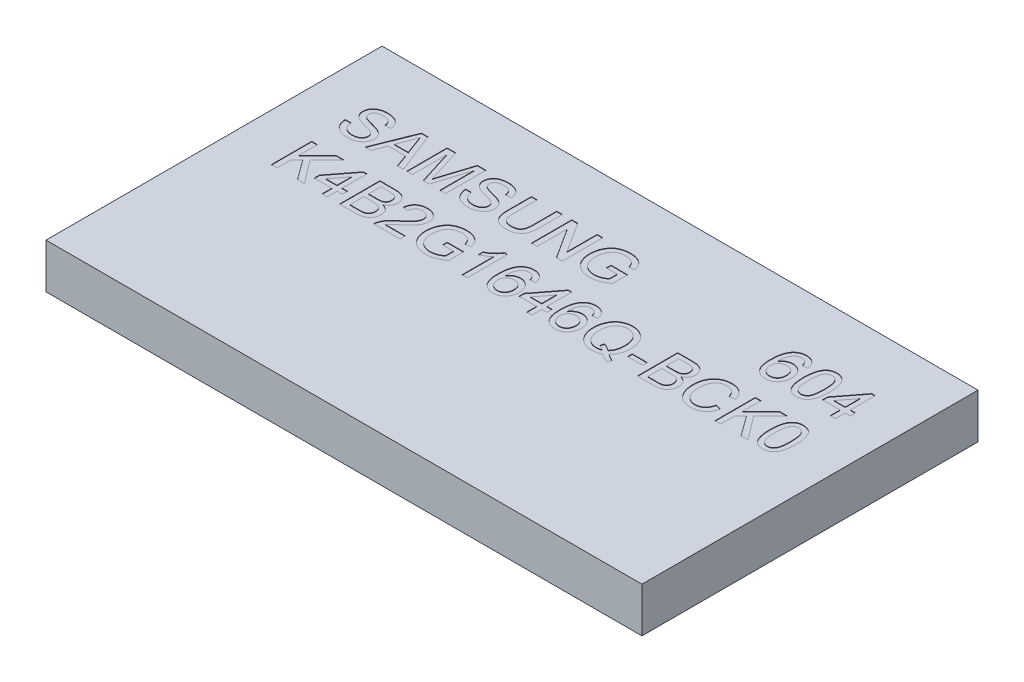
SolidWorks part; units mm, degrees
ref_plane "Спереди" through (0, 0, 0) normal (0, 0, 1) x (1, 0, 0)
ref_plane "Сверху" through (0, 0, 0) normal (0, 1, 0) x (1, 0, 0)
ref_plane "Справа" through (0, 0, 0) normal (1, 0, 0) x (0, 0, -1)
sketch "Эскиз1" plane through (0, 0, 0) normal (0, 1, 0) x (1, 0, 0)
  line L1 (6.65, -3.75) -> (-6.65, -3.75)
  line L2 (6.65, -3.75) -> (6.65, 3.75)
  line L3 (6.65, 3.75) -> (-6.65, 3.75)
  line L4 (-6.65, -3.75) -> (-6.65, 3.75)
  line L5 (6.65, -3.75) -> (-6.65, 3.75) construction
  line L6 (6.65, 3.75) -> (-6.65, -3.75) construction
  point P0 (0, 0)
  dimension "D1" = 13.3
  dimension "D2" = 7.5
extrude "Бобышка-Вытянуть1" add sketch "Эскиз1" along normal blind 1
sketch "Эскиз2" plane through (0, 1, 0) normal (0, 1, 0) x (1, 0, 0)
  text T0 "SAMSUNG         604\r\nK4B2G1646Q-BCK0" font "Arial" height 0.9
extrude "Вырез-Вытянуть1" cut sketch "Эскиз2" against normal blind 0.01
